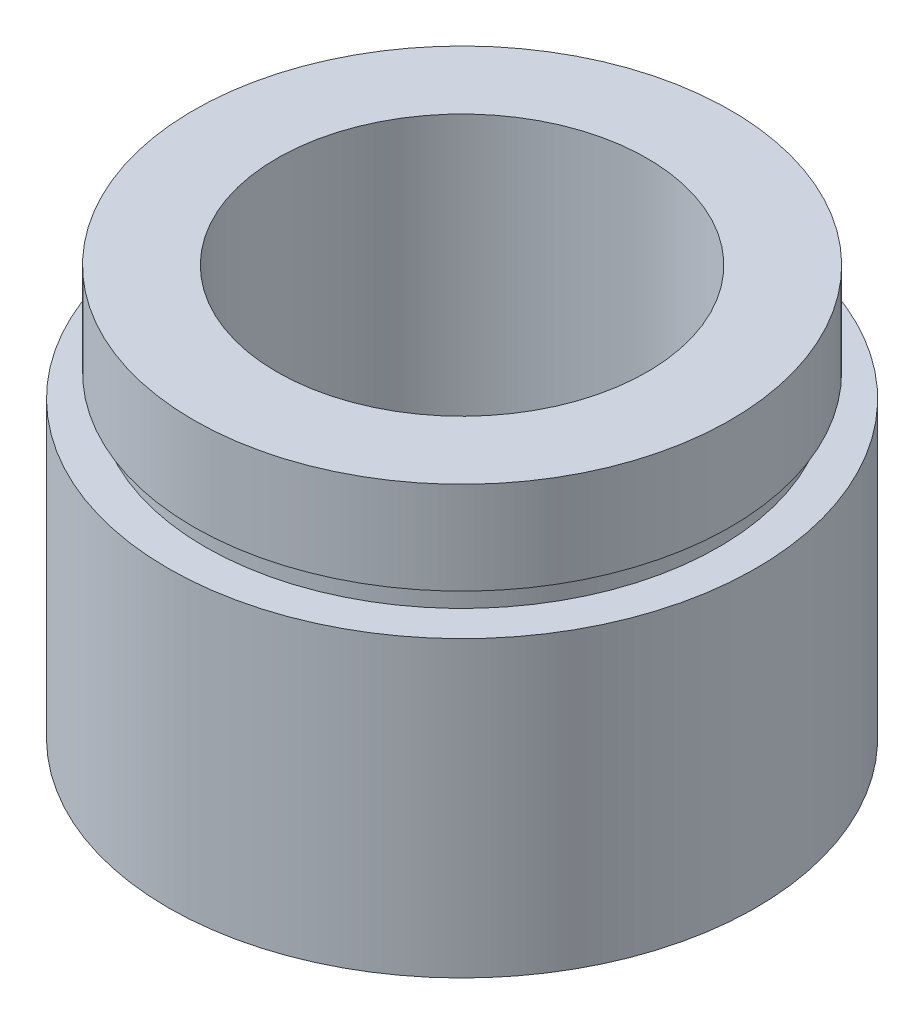
SolidWorks part; units mm, degrees
ref_plane "前视基准面" through (0, 0, 0) normal (0, 0, 1) x (1, 0, 0)
ref_plane "上视基准面" through (0, 0, 0) normal (0, 1, 0) x (1, 0, 0)
ref_plane "右视基准面" through (0, 0, 0) normal (1, 0, 0) x (0, 0, -1)
sketch "草图1" plane through (0, 0, 0) normal (0, 0, 1) x (1, 0, 0)
  line L0 (0, 161.3762) -> (0, 0) construction
  line L1 (141.7365, 0) -> (-131.7984, 0) construction
  line L2 (11.1, 0) -> (11.1, 4.5)
  line L3 (11.7, 4.5) -> (11.7, 5.5)
  line L4 (11.1, 4.5) -> (11.7, 4.5)
  line L5 (8, 5.5) -> (8, 17.7)
  line L6 (11.7, 5.5) -> (8, 5.5)
  line L7 (12.7, 0) -> (12.7, 12.7)
  line L8 (11.1, 0) -> (12.7, 0)
  line L9 (11.1, 12.7) -> (11.1, 13.7)
  line L10 (12.7, 12.7) -> (11.1, 12.7)
  line L11 (11.6, 13.7) -> (11.6, 17.7)
  line L12 (11.1, 13.7) -> (11.6, 13.7)
  line L13 (11.6, 17.7) -> (8, 17.7)
  dimension "D1" = 11.1
  dimension "D2" = 4.5
  dimension "D3" = 11.7
  dimension "D4" = 8
  dimension "D5" = 11.1
  dimension "D6" = 11.6
  dimension "D7" = 5
  dimension "D8" = 1
  dimension "D9" = 12.7
  dimension "D10" = 1
  dimension "D11" = 12.7
revolve "旋转1" add sketch "草图1" angle 360 about L0
cosmetic thread "装饰螺纹线1"
cosmetic thread "装饰螺纹线2"
cosmetic thread "装饰螺纹线3"
